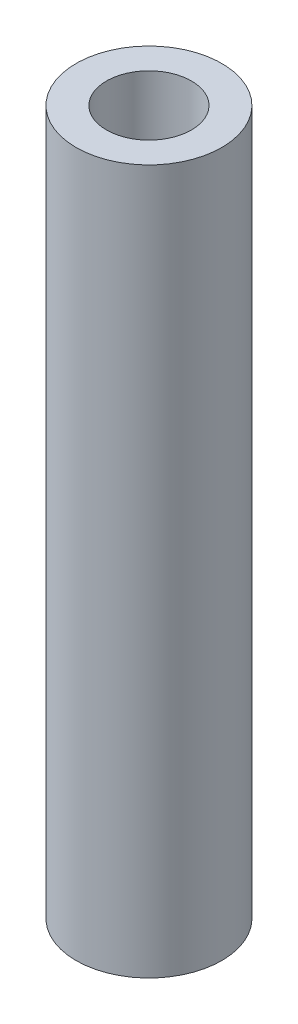
SolidWorks part; units mm, degrees
ref_plane "Front Plane" through (0, 0, 0) normal (0, 0, 1) x (1, 0, 0)
ref_plane "Top Plane" through (0, 0, 0) normal (0, 1, 0) x (1, 0, 0)
ref_plane "Right Plane" through (0, 0, 0) normal (1, 0, 0) x (0, 0, -1)
sketch "Sketch1" plane through (0, 0, 0) normal (0, 1, 0) x (1, 0, 0)
  circle A0 centre (0, 0) radius 3
  circle A1 centre (0, 0) radius 1.75
  dimension "D1" = 6
  dimension "D2" = 3.5
extrude "Boss-Extrude1" add sketch "Sketch1" along normal blind 29
